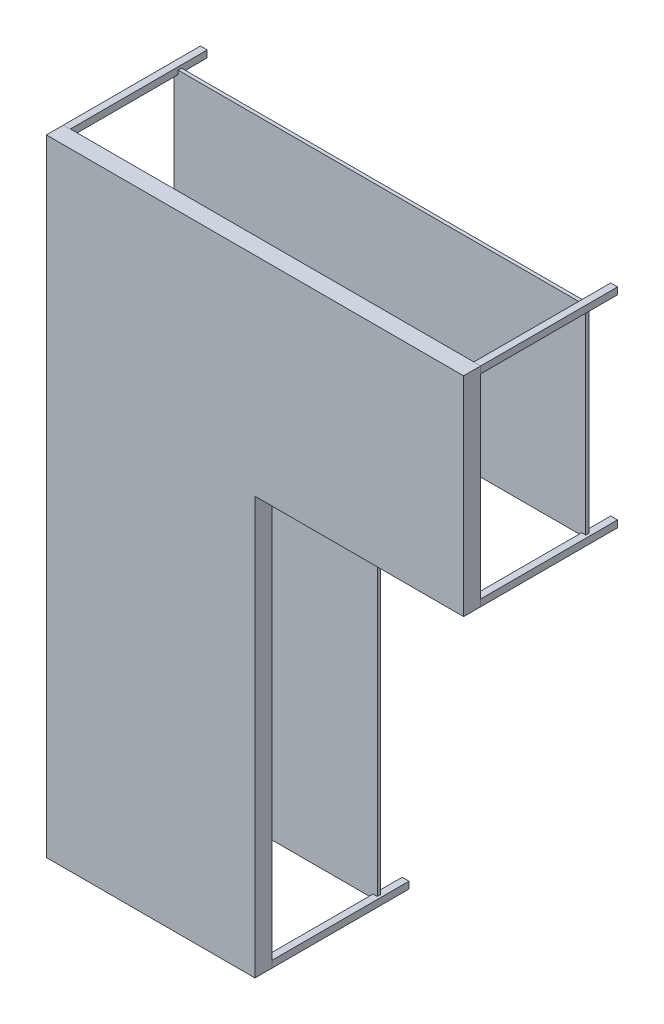
SolidWorks part; units mm, degrees
ref_plane "Front Plane" through (0, 0, 0) normal (0, 0, 1) x (1, 0, 0)
ref_plane "Top Plane" through (0, 0, 0) normal (0, 1, 0) x (1, 0, 0)
ref_plane "Right Plane" through (0, 0, 0) normal (1, 0, 0) x (0, 0, -1)
sketch "Sketch3" plane through (0, 0, 0) normal (0, 0, 1) x (1, 0, 0)
  line L0 (2438.4, -1219.2) -> (2438.4, 0)
  line L1 (0, 0) -> (2438.4, 0)
  line L2 (2438.4, -1219.2) -> (1219.2, -1219.2)
  line L3 (1219.2, -3657.6) -> (0, -3657.6)
  line L4 (0, 0) -> (0, -3657.6)
  line L5 (1219.2, -1219.2) -> (1219.2, -3657.6)
  dimension "D1" = 2438.4
  dimension "D2" = 1219.2
  dimension "D3" = 1219.2
  dimension "D4" = 2438.4
extrude "Boss-Extrude1" add sketch "Sketch3" along normal blind 100
sketch "Sketch4" plane through (0, 0, 0) normal (0, 0, -1) x (-1, 0, 0)
  line L0 (-2398.4, -40) -> (-2438.4, -40)
  line L1 (0, -3657.6) -> (-40, -3657.6)
  line L2 (0, -3657.6) -> (0, -3617.6)
  line L3 (0, -3617.6) -> (-40, -3617.6)
  line L4 (-40, -3657.6) -> (-40, -3617.6)
  line L5 (-2398.4, -40) -> (-2398.4, 0)
  line L6 (-2398.4, 0) -> (-2438.4, 0)
  line L7 (-2438.4, -40) -> (-2438.4, 0)
  line L8 (0, -40) -> (-40, -40)
  line L9 (0, -40) -> (0, 0)
  line L10 (0, 0) -> (-40, 0)
  line L11 (-40, -40) -> (-40, 0)
  line L13 (-1179.2, -3657.6) -> (-1219.2, -3657.6)
  line L14 (-1179.2, -3657.6) -> (-1179.2, -3617.6)
  line L15 (-1179.2, -3617.6) -> (-1219.2, -3617.6)
  line L16 (-1219.2, -3657.6) -> (-1219.2, -3617.6)
  line L17 (-1179.2, -1219.2) -> (-1219.2, -1219.2)
  line L18 (-1179.2, -1219.2) -> (-1179.2, -1179.2)
  line L19 (-1179.2, -1179.2) -> (-1219.2, -1179.2)
  line L20 (-1219.2, -1219.2) -> (-1219.2, -1179.2)
  line L21 (-2398.4, -1219.2) -> (-2438.4, -1219.2)
  line L22 (-2398.4, -1219.2) -> (-2398.4, -1179.2)
  line L23 (-2398.4, -1179.2) -> (-2438.4, -1179.2)
  line L24 (-2438.4, -1219.2) -> (-2438.4, -1179.2)
  line L25 (0, -1219.2) -> (-40, -1219.2)
  line L26 (0, -1219.2) -> (0, -1179.2)
  line L27 (0, -1179.2) -> (-40, -1179.2)
  line L28 (-40, -1219.2) -> (-40, -1179.2)
  line L29 (0, 0) -> (0, -3657.6) construction
  dimension "D1" = 40
  dimension "D2" = 40
  dimension "D3" = 40
  dimension "D4" = 40
  dimension "D5" = 40
  dimension "D6" = 40
  dimension "D7" = 40
  dimension "D8" = 40
  dimension "D9" = 40
  dimension "D10" = 40
  dimension "D11" = 40
  dimension "D12" = 40
  dimension "D13" = 40
  dimension "D14" = 40
extrude "Boss-Extrude2" add sketch "Sketch4" along normal blind 800 separate body
sketch "Sketch5" plane through (0, 0, 0) normal (0, 0, -1) x (-1, 0, 0)
  line L0 (0, -3657.6) -> (-1219.2, -3657.6) construction
  line L3 (0, 0) -> (0, -3657.6) construction
  line L4 (-2438.4, 0) -> (0, 0) construction
  line L5 (-2438.4, -1219.2) -> (-2438.4, 0) construction
  circle A0 centre (-600, -2897.6) radius 60
  circle A1 centre (-600, -2137.6) radius 60
  circle A2 centre (-1588.4, -600) radius 60
  circle A4 centre (-738.4, -600) radius 60
  dimension "D1" = 120
  dimension "D4" = 600
  dimension "D3" = 850
  dimension "D5" = 120
  dimension "D6" = 760
  dimension "D7" = 760
  dimension "D2" = 120
  dimension "D8" = 600
  dimension "D9" = 600
  dimension "D10" = 120
  dimension "D11" = 850
extrude "Cut-Extrude2" [suppressed] cut sketch "Sketch5" against normal through all
ref_plane "Plane1" through (0, 0, -650) normal (0, 0, -1) x (-1, 0, 0)
sketch "Sketch6" plane through (0, 0, -650) normal (0, 0, -1) x (-1, 0, 0)
  line L1 (-15.9239, -1205.1278) -> (-1203.8896, -1205.1278)
  line L2 (-15.9239, -1205.1278) -> (-15.9239, -3639.639)
  line L3 (-15.9239, -3639.639) -> (-1203.8896, -3639.639)
  line L4 (-1203.8896, -1205.1278) -> (-1203.8896, -3639.639)
  line L5 (-2422.1991, -1193.1927) -> (-15.9239, -1193.1927)
  line L6 (-2422.1991, -1193.1927) -> (-2422.1991, -17.2001)
  line L7 (-2422.1991, -17.2001) -> (-15.9239, -17.2001)
  line L8 (-15.9239, -1193.1927) -> (-15.9239, -17.2001)
extrude "Boss-Extrude3" add sketch "Sketch6" against normal blind 20 separate body contours L1 L8 L7 L6 L5 | L1 L4 L3 L2
equation "\"VV\"=40"
equation "\"D2@Sketch4\"=\"VV\""
equation "\"D1@Sketch4\"=\"VV\""
equation "\"D7@Sketch4\"=\"VV\""
equation "\"D8@Sketch4\"=\"VV\""
equation "\"D10@Sketch4\"=\"VV\""
equation "\"D14@Sketch4\"=\"VV\""
equation "\"D13@Sketch4\"=\"VV\""
equation "\"D6@Sketch4\"=\"VV\""
equation "\"D5@Sketch4\"=\"VV\""
equation "\"D9@Sketch4\"=\"VV\""
equation "\"D12@Sketch4\"=\"VV\""
equation "\"D11@Sketch4\"=\"VV\""
equation "\"D4@Sketch4\"=\"VV\""
equation "\"D3@Sketch4\"=\"VV\""
